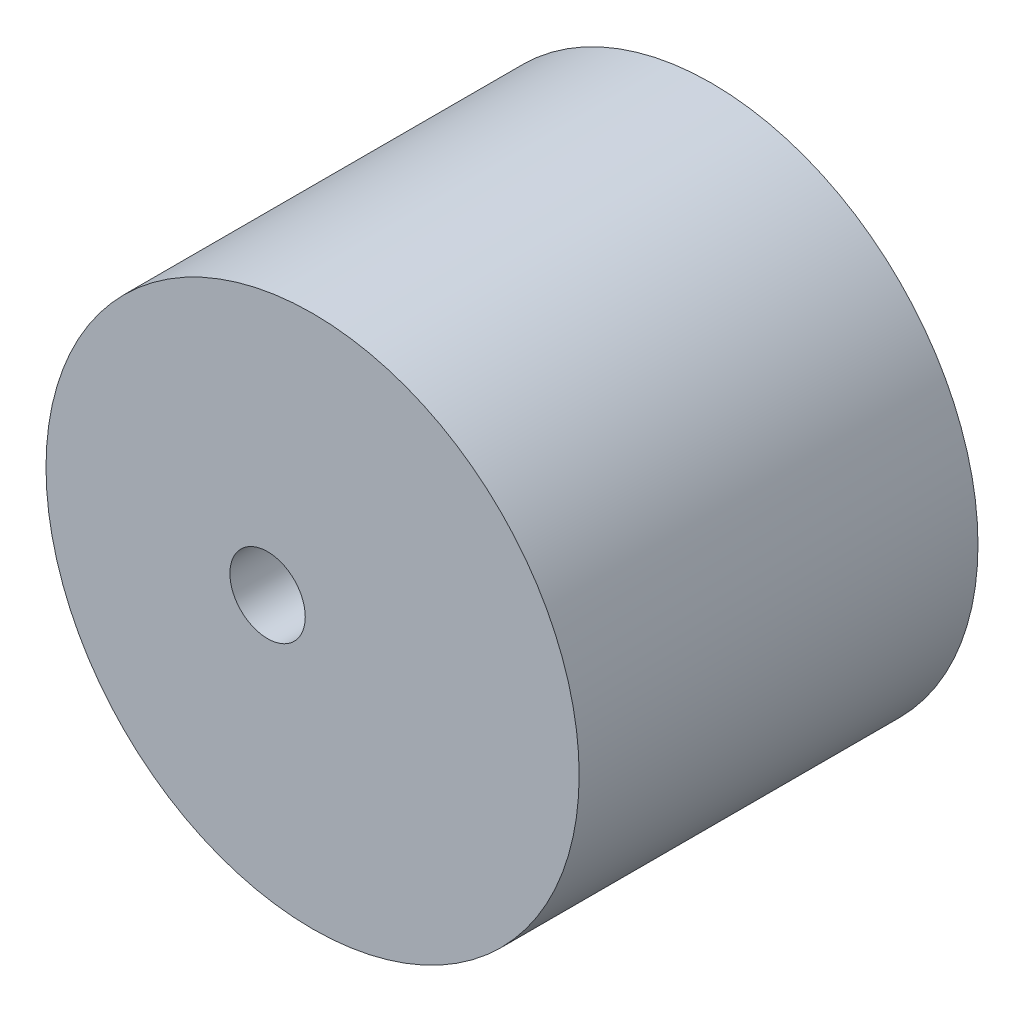
SolidWorks part; units mm, degrees
ref_plane "Front Plane" through (0, 0, 0) normal (0, 0, 1) x (1, 0, 0)
ref_plane "Top Plane" through (0, 0, 0) normal (0, 1, 0) x (1, 0, 0)
ref_plane "Right Plane" through (0, 0, 0) normal (1, 0, 0) x (0, 0, -1)
sketch "Sketch11" plane through (0, 0, 0) normal (0, 0, 1) x (1, 0, 0)
  circle A0 centre (0, 0) radius 23.3938
  circle A1 centre (-3.95, 0) radius 3.3085
  point P4 (0, 0)
extrude "Boss-Extrude13" add sketch "Sketch11" along normal blind 35
